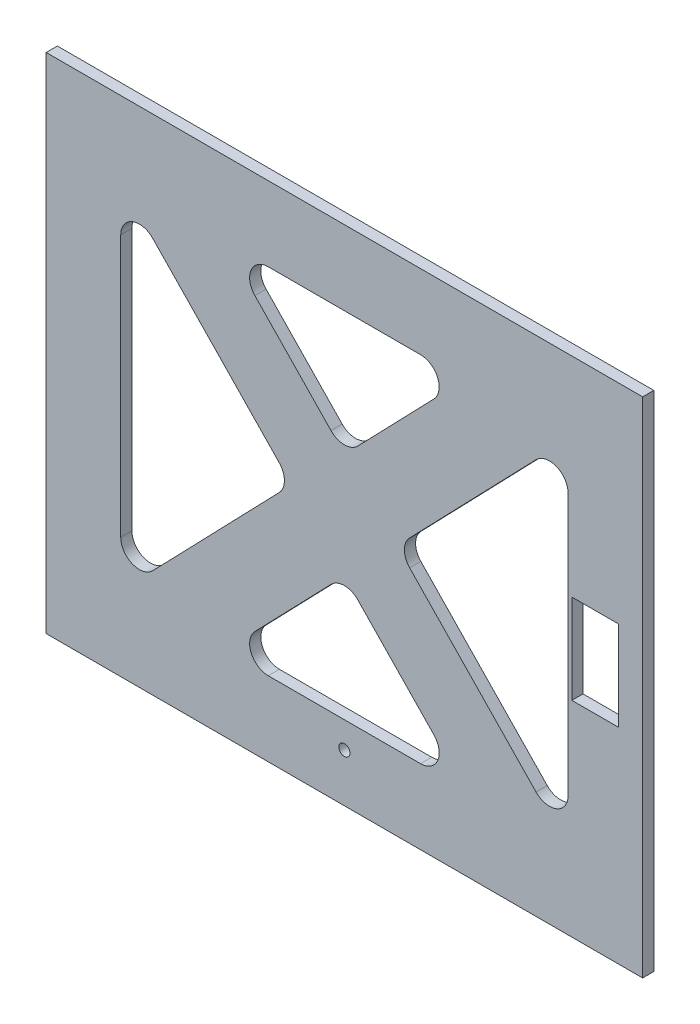
SolidWorks part; units mm, degrees
material "birch 3mm plywood"
ref_plane "Front Plane" through (0, 0, 0) normal (0, 0, 1) x (1, 0, 0)
ref_plane "Top Plane" through (0, 0, 0) normal (0, 1, 0) x (1, 0, 0)
ref_plane "Right Plane" through (0, 0, 0) normal (1, 0, 0) x (0, 0, -1)
sketch "Sketch1" plane through (0, 0, 152) normal (0, 0, 1) x (1, 0, 0)
  line L1 (-80, 80.4171) -> (80, 80.4171)
  line L2 (-80, 80.4171) -> (-80, -54.5829)
  line L3 (-80, -54.5829) -> (80, -54.5829)
  line L4 (80, 80.4171) -> (80, -54.5829)
  line L6 (-60, -22.2046) -> (-60, 48.0389)
  line L7 (-51.4028, 51.5116) -> (-17.4968, 16.3899)
  line L12 (78, -49.5829) -> (-78, -49.5829) construction
  line L13 (78, 75.4171) -> (78, -49.5829) construction
  line L14 (-78, -49.5829) -> (-78, 75.4171) construction
  line L15 (-78, 75.4171) -> (78, 75.4171) construction
  line L18 (20.4243, 60.4171) -> (-20.4243, 60.4171)
  line L19 (-17.4968, 9.4444) -> (-51.4028, -25.6773)
  line L20 (-24.0216, 51.9444) -> (-3.5972, 30.7877)
  line L21 (3.5972, 30.7877) -> (24.0216, 51.9444)
  line L22 (80, 80.4171) -> (80, 77.4171) construction
  line L23 (51.4028, 51.5116) -> (17.4968, 16.3899)
  line L24 (60, -22.2046) -> (60, 48.0389)
  line L25 (17.4968, 9.4444) -> (51.4028, -25.6773)
  line L26 (-78, 12.9171) -> (78, 12.9171) construction
  line L27 (-24.0216, -26.1101) -> (-3.5972, -4.9534)
  line L28 (20.4243, -34.5829) -> (-20.4243, -34.5829)
  line L29 (3.5972, -4.9534) -> (24.0216, -26.1101)
  line L30 (0, 27.0615) -> (0, -1.2272) construction
  line L31 (-14.1443, 12.9171) -> (14.1443, 12.9171) construction
  line L32 (0, 27.0615) -> (0, -1.2272) construction
  line L34 (-80, -54.5829) -> (-80, 77.4171) construction
  line L36 (80, 80.4171) -> (-80, 80.4171) construction
  line L37 (75, -49.5829) -> (-75, -49.5829) construction
  arc A0 (-51.4028, -25.6773) -> (-60, -22.2046) centre (-55, -22.2046) cw
  arc A1 (-17.4968, 9.4444) -> (-17.4968, 16.3899) centre (-21.0941, 12.9171) ccw
  arc A2 (-51.4028, 51.5116) -> (-60, 48.0389) centre (-55, 48.0389) ccw
  arc A3 (24.0216, -26.1101) -> (20.4243, -34.5829) centre (20.4243, -29.5829) cw
  arc A4 (-24.0216, -26.1101) -> (-20.4243, -34.5829) centre (-20.4243, -29.5829) ccw
  arc A5 (-3.5972, -4.9534) -> (3.5972, -4.9534) centre (0, -8.4261) cw
  arc A6 (17.4968, 16.3899) -> (17.4968, 9.4444) centre (21.0941, 12.9171) ccw
  arc A7 (51.4028, -25.6773) -> (60, -22.2046) centre (55, -22.2046) ccw
  arc A8 (60, 48.0389) -> (51.4028, 51.5116) centre (55, 48.0389) ccw
  arc A9 (-24.0216, 51.9444) -> (-20.4243, 60.4171) centre (-20.4243, 55.4171) cw
  arc A10 (24.0216, 51.9444) -> (20.4243, 60.4171) centre (20.4243, 55.4171) ccw
  arc A11 (3.5972, 30.7877) -> (-3.5972, 30.7877) centre (0, 34.2604) cw
  point P14 (0, 12.9171)
  point P15 (0, 12.9171)
  point P32 (-60, 60.4171)
  point P35 (32.201, -34.5829)
  point P38 (-32.201, -34.5829)
  point P51 (-32.201, 60.4171)
  point P54 (32.201, 60.4171)
  dimension "D9" = 5
  dimension "D10" = 5
  dimension "D1" = 2
  dimension "D2" = 2
  dimension "D3" = 5
  dimension "D4" = 5
  dimension "D5" = 20
  dimension "D6" = 20
  dimension "D7" = 20
  dimension "D8" = 20
extrude "Boss-Extrude1" add sketch "Sketch1" along normal blind 3
sketch "Sketch2" plane through (0, 0, 155) normal (0, 0, 1) x (1, 0, 0)
  line L0 (-80, -41.6319) -> (80, -41.6319)
  line L1 (-80, 80.4171) -> (-80, -54.5829) construction
  line L2 (80, -54.5829) -> (80, 80.4171) construction
  circle A0 centre (0, -41.6319) radius 1.5
extrude "Cut-Extrude1" cut sketch "Sketch2" against normal blind 20 contours L0 A0 | L0 A0
ref_plane "Plane1" through (80, -54.5829, 155) normal (0, 0, -1) x (-1, 0, 0)
sketch "Sketch3" plane through (80, -54.5829, 155) normal (0, 0, -1) x (-1, 0, 0)
  line L0 (0, 0) -> (8, 0)
  line L1 (160, 0) -> (0, 0) construction
  line L2 (8, 0) -> (8, 54.9)
  line L4 (8, 54.9) -> (18, 54.9)
  line L5 (8, 54.9) -> (8, 75.1)
  line L6 (8, 75.1) -> (18, 75.1)
  line L7 (18, 54.9) -> (18, 75.1)
  dimension "D1" = 20.2
  dimension "D2" = 10
extrude "Cut-Extrude2" cut sketch "Sketch3" along normal blind 10 contours L4 L7 L6 L5
sketch "Sketch5" plane through (0, 0.3171, 0) normal (0, 1, 0) x (1, 0, 0)
  line L0 (72, -152) -> (72, -155)
  line L1 (72, -155) -> (62, -155)
  line L2 (62, -155) -> (62, -152)
  line L3 (62, -152) -> (62, -155) construction
  line L4 (62, -152) -> (72, -152)
extrude "Boss-Extrude2" add sketch "Sketch5" along normal blind 30
sketch "Sketch6" plane through (0, 0, 155) normal (0, 0, 1) x (1, 0, 0)
  line L0 (80, -54.5829) -> (72, -54.5829)
  line L1 (-80, -54.5829) -> (80, -54.5829) construction
  line L2 (72, -54.5829) -> (72, 4.3171)
  line L4 (72, 4.3171) -> (62, 4.3171)
  line L5 (72, 4.3171) -> (72, 24.4671)
  line L6 (72, 24.4671) -> (62, 24.4671)
  line L7 (62, 4.3171) -> (62, 24.4671)
  dimension "D1" = 10
  dimension "D2" = 20.15
extrude "Cut-Extrude3" cut sketch "Sketch6" against normal blind 30 contours L7 L4 L5 L6
sketch "Sketch7" plane through (0, 4.3171, 0) normal (0, 1, 0) x (1, 0, 0)
  line L0 (62, -155) -> (62, -152)
  line L1 (62, -152) -> (72, -152)
  line L2 (72, -151.5923) -> (72, -155)
  line L3 (72, -155) -> (62, -155)
  line M1 (72, -152) -> (62, -152)
  line M2 (62, -152) -> (62, -155)
  line M3 (62, -155) -> (72, -155)
  line M4 (72, -155) -> (72, -152)
extrude "Boss-Extrude3" add sketch "Sketch7" along normal blind 30 contours M4 M1 M2 M3
sketch "Sketch8" plane through (0, 0, 155) normal (0, 0, 1) x (1, 0, 0)
  line L0 (80, -54.5829) -> (73.4372, -54.5829)
  line L1 (-80, -54.5829) -> (80, -54.5829) construction
  line L2 (73.4372, -54.5829) -> (73.4372, 5.0045)
  line L4 (67.6872, 15.7545) -> (79.1872, 15.7545)
  line L5 (67.6872, 15.7545) -> (67.6872, -5.7455)
  line L6 (67.6872, -5.7455) -> (79.1872, -5.7455)
  line L7 (79.1872, 15.7545) -> (79.1872, -5.7455)
  line L8 (67.6872, 15.7545) -> (79.1872, -5.7455) construction
  line L9 (67.6872, -5.7455) -> (79.1872, 15.7545) construction
  dimension "D1" = 21.5
  dimension "D2" = 11.5
extrude "Cut-Extrude4" cut sketch "Sketch8" against normal blind 10
sketch "Sketch9" plane through (0, -5.7455, 0) normal (0, 1, 0) x (1, 0, 0)
  line L0 (67.6872, -155) -> (79.1872, -155)
  line L1 (67.6872, -155) -> (67.6872, -152)
  line L2 (67.6872, -152) -> (79.1872, -152) construction
  line L3 (67.6872, -152) -> (67.6872, -155) construction
  line L4 (67.6872, -152) -> (79.1872, -152)
  line L5 (79.1872, -152) -> (79.1872, -155.2641)
extrude "Boss-Extrude5" add sketch "Sketch9" along normal blind 30 contours L3 L0 L1 L2
sketch "Sketch10" plane through (0, 0, 155) normal (0, 0, 1) x (1, 0, 0)
  line L0 (80, -54.5829) -> (72, -54.5829)
  line L1 (-80, -54.5829) -> (80, -54.5829) construction
  line L2 (72, -54.5829) -> (72, 0.4171)
  line L4 (72, 0.4171) -> (61, 0.4171)
  line L5 (72, 0.4171) -> (72, 21.4171)
  line L6 (72, 21.4171) -> (61, 21.4171)
  line L7 (61, 0.4171) -> (61, 21.4171)
  dimension "D1" = 21
  dimension "D2" = 11
extrude "Cut-Extrude5" cut sketch "Sketch10" against normal blind 30 contours L7 L4 L5 L6
sketch "Sketch11" plane through (72, 0, 0) normal (-1, 0, 0) x (0, 0, 1)
  line L0 (152, 0.4171) -> (155, 0.4171)
  line L1 (155, 0.4171) -> (155, 21.4171)
  line L2 (155, 21.4171) -> (152, 21.4171)
  line L3 (152, 21.4171) -> (152, 0.4171)
extrude "Cut-Extrude6" cut sketch "Sketch11" against normal blind 1.5
sketch "Sketch12" plane through (0, 21.4171, 0) normal (0, -1, 0) x (-1, 0, 0)
  line L0 (-73.5, -152) -> (-73.5, -155)
  line L1 (-73.5, -155) -> (-61, -155)
  line L2 (-61, -155) -> (-61, -152)
  line L3 (-61, -152) -> (-73.5, -152)
extrude "Cut-Extrude7" cut sketch "Sketch12" against normal blind 3
